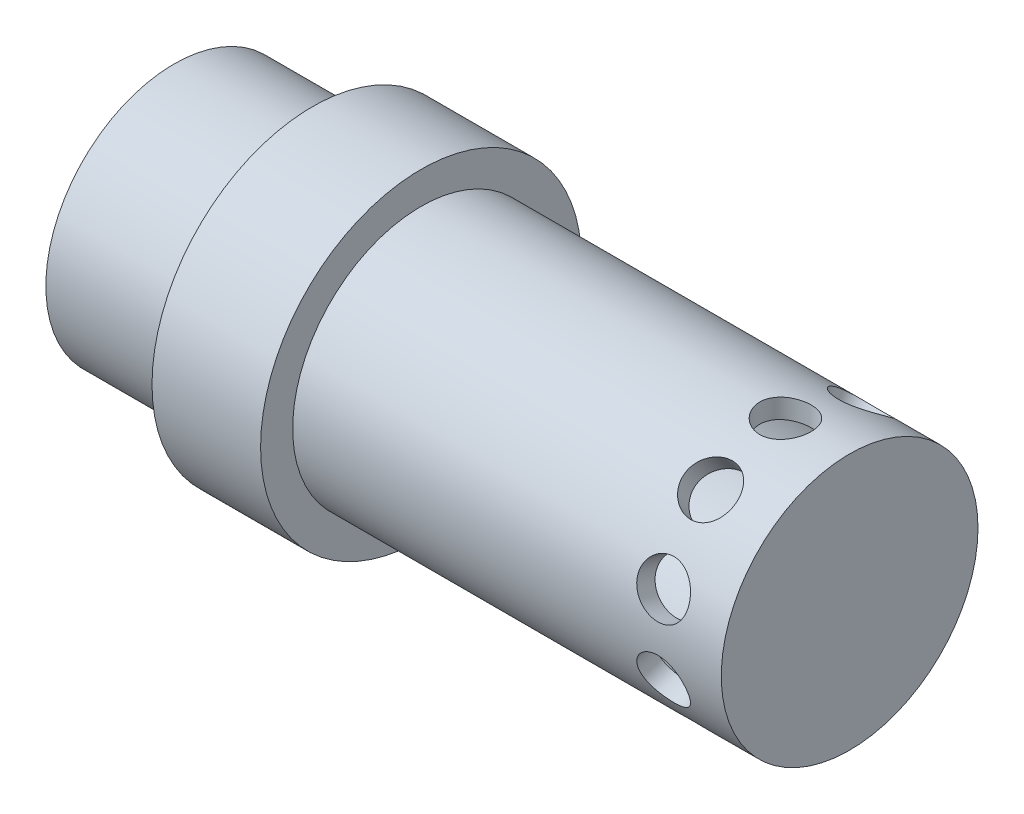
SolidWorks part; units mm, degrees
ref_plane "Front Plane" through (0, 0, 0) normal (0, 0, 1) x (1, 0, 0)
ref_plane "Top Plane" through (0, 0, 0) normal (0, 1, 0) x (1, 0, 0)
ref_plane "Right Plane" through (0, 0, 0) normal (1, 0, 0) x (0, 0, -1)
sketch "CL" plane through (0, 0, 0) normal (0, 0, 1) x (1, 0, 0)
  line L0 (27.575, 0) -> (-130.7221, 0) construction
  point P3 (0, 0)
sketch "Sketch1" plane through (0, 0, 0) normal (0, 0, 1) x (1, 0, 0)
  line L0 (0, 0) -> (0, 20)
  line L2 (0, 20) -> (-66.7844, 20)
  line L4 (-83.703, 20) -> (-105.2449, 20)
  line L5 (-105.2449, 20) -> (-105.2449, 17)
  line L6 (-105.2449, 17) -> (-3, 17)
  line L7 (-3, 17) -> (-3, 0)
  line L8 (-3, 0) -> (0, 0)
  line L9 (-66.7844, 20) -> (-66.7844, 25)
  line L10 (-66.7844, 25) -> (-83.703, 25)
  line L11 (-83.703, 25) -> (-83.703, 20)
  dimension "D1" = 20
  dimension "D2" = 3
  dimension "D3" = 3
  dimension "D4" = 5
revolve "Revolve1" add sketch "Sketch1" angle 360 about L0
sketch "Sketch2" plane through (0, 0, 0) normal (0, 1, 0) x (1, 0, 0)
  line L0 (0, 0) -> (-10, 0) construction
  circle A0 centre (-10, 0) radius 4
  dimension "D1" = 8
  dimension "D2" = 10
extrude "Cut-Extrude1" cut sketch "Sketch2" along normal up to next
pattern_circular "CirPattern1" count 10 over 360 about axis through (27.575, 0, 0) along (-1, 0, 0) of "Cut-Extrude1"
equation "\"thick\"= 3mm"
equation "\"piston_rad\"= 20mm"
equation "\"D2@Sketch1\"=\"thick\""
equation "\"D1@Sketch1\"=\"piston_rad\""
equation "\"D3@Sketch1\"=\"thick\""
equation "\"spring_lip\"= 5mm"
equation "\"D4@Sketch1\"=\"spring_lip\""
equation "\"injector_dia\"= 8mm"
equation "\"D1@Sketch2\"=\"injector_dia\""
equation "\"injector_hole_offset\"= 10mm"
equation "\"D2@Sketch2\"=\"injector_hole_offset\""
